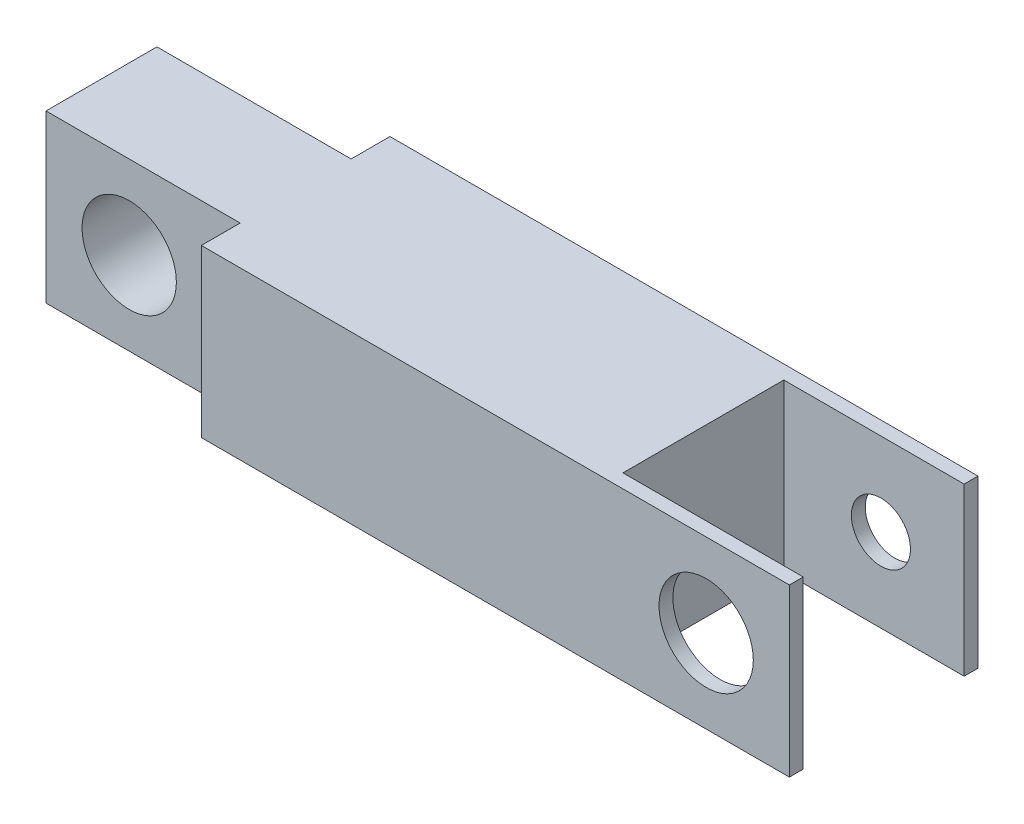
SolidWorks part; units mm, degrees
ref_plane "Front Plane" through (0, 0, 0) normal (0, 0, 1) x (1, 0, 0)
ref_plane "Top Plane" through (0, 0, 0) normal (0, 1, 0) x (1, 0, 0)
ref_plane "Right Plane" through (0, 0, 0) normal (1, 0, 0) x (0, 0, -1)
sketch "Sketch1" plane through (0, 0, 0) normal (0, 0, 1) x (1, 0, 0)
  line L0 (-39.0971, 4.4382) -> (-39.0971, -3.1818)
  line L1 (-39.0971, -3.1818) -> (-3.2831, -3.1818)
  line L2 (-3.2831, -3.1818) -> (-3.2831, 4.4382)
  line L3 (-3.2831, 4.4382) -> (-39.0971, 4.4382)
  dimension "D1" = 7.62
  dimension "D2" = 35.814
extrude "Boss-Extrude1" add sketch "Sketch1" along normal blind 8.636
sketch "Sketch2" plane through (0, 0, 8.636) normal (0, 0, 1) x (1, 0, 0)
  line L0 (-3.2831, -3.1818) -> (-3.2831, 4.4382) construction
  point P0 (-35.2871, 0.6282)
  point P1 (-7.0931, 0.6282)
  point P2 (0, 0)
  point P4 (0, 0)
  point P5 (0, 0)
  point P7 (0, 0)
  point P8 (0, 0)
  point P9 (0, 0)
  dimension "D1" = 28.194
  dimension "D2" = 3.81
sketch "Sketch4" plane through (0, 4.4382, 0) normal (0, 1, 0) x (1, 0, 0)
  line L0 (-39.0971, 0) -> (-30.2071, 0)
  line L1 (-3.2831, 0) -> (-39.0971, 0) construction
  line L2 (-30.2071, 0) -> (-30.2071, -1.778)
  line L3 (-30.2071, -1.778) -> (-39.0971, -1.778)
  line L4 (-39.0971, -8.636) -> (-39.0971, 0) construction
  line L5 (-39.0971, -1.778) -> (-39.0971, -6.858)
  line L6 (-39.0971, -6.858) -> (-30.2071, -6.858)
  line L7 (-30.2071, -6.858) -> (-30.2071, -8.636)
  line L8 (-3.2831, -8.636) -> (-39.0971, -8.636) construction
  line L9 (-30.2071, -8.636) -> (-39.0971, -8.636)
  line L10 (-39.0971, -8.636) -> (-39.0971, 0)
  line M5 (-3.2831, 0) -> (-39.0971, 0)
  line M6 (-39.0971, 0) -> (-39.0971, -8.636)
  line M7 (-39.0971, -8.636) -> (-3.2831, -8.636)
  dimension "D1" = 8.89
  dimension "D2" = 8.89
  dimension "D3" = 5.08
  dimension "D4" = 1.778
extrude "Cut-Extrude1" cut sketch "Sketch4" against normal through all contours L3 L2 M5 M6 | L7 L6 M6 M7
sketch "Sketch6" plane through (0, 4.4382, 0) normal (0, 1, 0) x (1, 0, 0)
  line L0 (-3.2831, -0.635) -> (-11.5381, -0.635)
  line L1 (-3.2831, -8.636) -> (-3.2831, 0) construction
  line L2 (-11.5381, -0.635) -> (-11.5381, -8.001)
  line L3 (-11.5381, -8.001) -> (-3.2831, -8.001)
  line L4 (-3.2831, -8.001) -> (-3.2831, -0.635)
  line L5 (-3.2831, 0) -> (-30.2071, 0) construction
  dimension "D1" = 8.255
  dimension "D2" = 7.366
  dimension "D3" = 0.635
extrude "Cut-Extrude2" cut sketch "Sketch6" against normal through all
sketch "Sketch7" plane through (0, 0, 6.858) normal (0, 0, 1) x (1, 0, 0)
  circle A0 centre (-35.2871, 0.6282) radius 2.159
extrude "Cut-Extrude3" cut sketch "Sketch7" against normal through all
sketch "Sketch8" plane through (0, 0, 8.636) normal (0, 0, 1) x (1, 0, 0)
  circle A0 centre (-7.0931, 0.6282) radius 2.159
extrude "Cut-Extrude4" cut sketch "Sketch8" against normal up to next
hole_wizard "#6-32 Tapped Hole1" positions "Sketch9" profile "Sketch10" tap size "#6-32" standard "ANSI Inch" end condition up to next
sketch "Sketch9" plane through (0, 0, 0) normal (0, 0, -1) x (-1, 0, 0)
  point P0 (7.0931, 0.6282)
sketch "Sketch10" plane through (-7.0931, 0.6282, 0) normal (1, 0, 0) x (0, 1, 0)
  line L0 (0, 0) -> (0, 0.635)
  line L1 (0, 0.635) -> (1.3525, 0.635)
  line L2 (1.3525, 0.635) -> (1.3525, 0)
  line L5 (1.3525, 0) -> (0, 0)
  line L11 (0, -6.35) -> (0, 107.95) construction
  dimension "Thread Major Dia." = 2.7051
  dimension "Thru Tap Drill Depth" = 0.635
ref_plane "Plane1" through (0, 0.6282, 0) normal (0, 1, 0) x (1, 0, 0)
ref_plane "Plane2" through (0, 0, 4.318) normal (0, 0, -1) x (-1, 0, 0)
